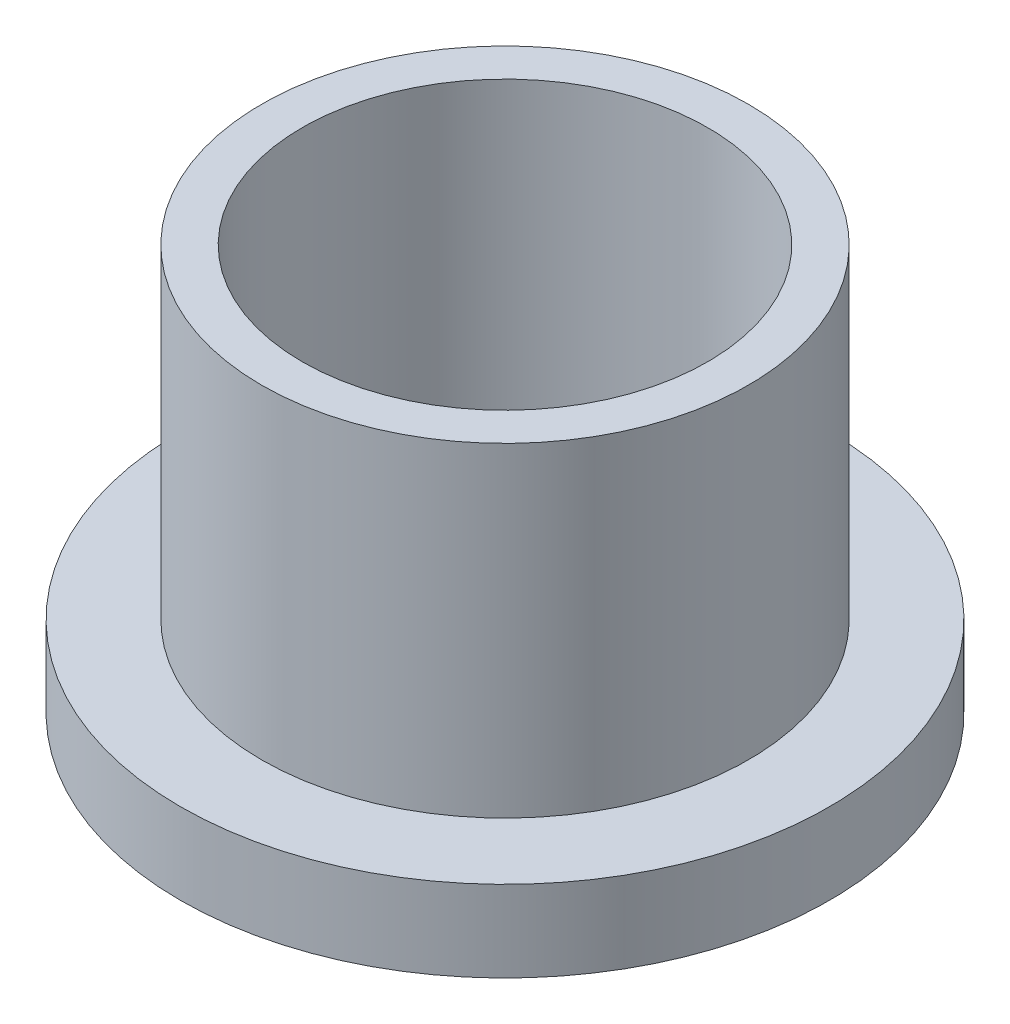
SolidWorks part; units mm, degrees
ref_plane "Front" through (0, 0, 0) normal (0, 0, 1) x (1, 0, 0)
ref_plane "Top" through (0, 0, 0) normal (0, 1, 0) x (1, 0, 0)
ref_plane "Right" through (0, 0, 0) normal (1, 0, 0) x (0, 0, -1)
sketch "Sketch1" plane through (0, 0, 0) normal (0, 1, 0) x (1, 0, 0)
  circle A0 centre (0, 0) radius 7.9375
  circle A1 centre (0, 0) radius 9.525
  circle A2 centre (0, 0) radius 12.7
  dimension "ID" = 15.875
  dimension "OD" = 19.05
  dimension "FlangeOD" = 25.4
sketch "Sketch2" plane through (0, 0, 0) normal (0, 1, 0) x (1, 0, 0)
  circle A0 centre (0, 0) radius 7.9375 construction
  circle A1 centre (0, 0) radius 9.525 construction
  circle A2 centre (0, 0) radius 7.9375
  circle A3 centre (0, 0) radius 9.525
extrude "Boss-Extrude1" add sketch "Sketch2" along normal blind 15.875
sketch "Sketch3" plane through (0, 0, 0) normal (0, 1, 0) x (1, 0, 0)
  circle A0 centre (0, 0) radius 12.7 construction
  circle A1 centre (0, 0) radius 9.525 construction
  circle A2 centre (0, 0) radius 12.7
  circle A3 centre (0, 0) radius 9.525
extrude "Boss-Extrude2" add sketch "Sketch3" along normal blind 3.175
